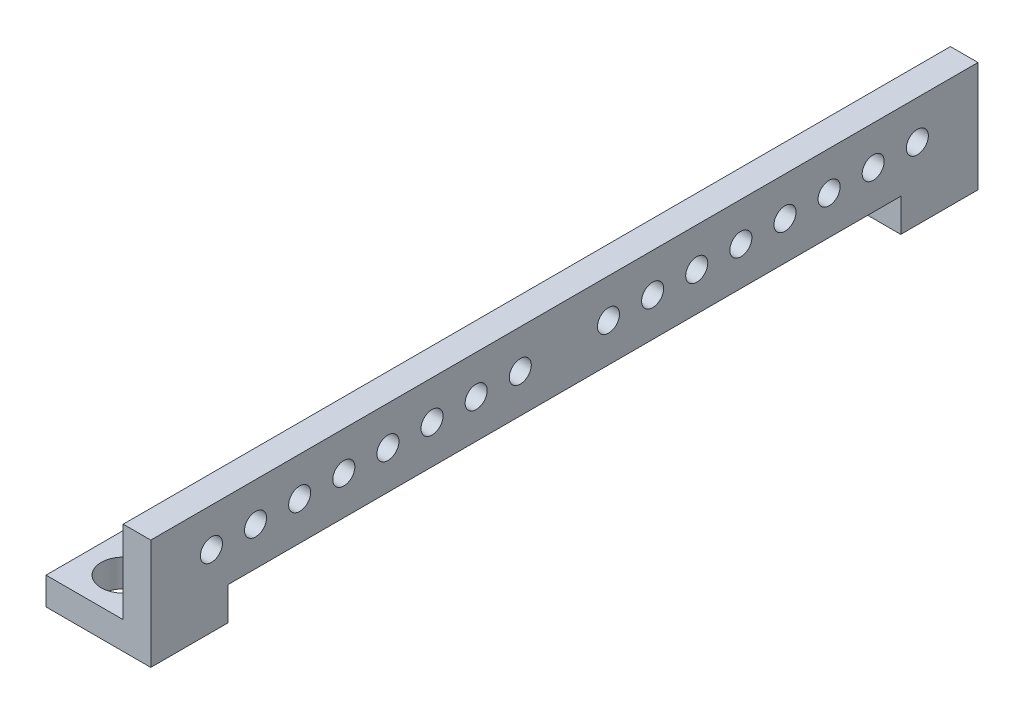
SolidWorks part; units mm, degrees
ref_plane "Front Plane" through (0, 0, 0) normal (0, 0, 1) x (1, 0, 0)
ref_plane "Top Plane" through (0, 0, 0) normal (0, 1, 0) x (1, 0, 0)
ref_plane "Right Plane" through (0, 0, 0) normal (1, 0, 0) x (0, 0, -1)
sketch "Sketch1" plane through (0, 0, 0) normal (1, 0, 0) x (0, 0, -1)
  line L0 (61, 0) -> (75, 0)
  line L1 (-75, 0) -> (-61, 0)
  line L2 (-75, 0) -> (-75, 20)
  line L3 (-75, 20) -> (75, 20)
  line L4 (75, 0) -> (75, 20)
  line L6 (-61, 0) -> (-61, 6)
  line L7 (-61, 6) -> (61, 6)
  line L8 (61, 0) -> (61, 6)
  line L12 (70, 13) -> (-70, 13) construction
  circle A2 centre (-16, 13) radius 2
  circle A3 centre (-24, 13) radius 2
  circle A4 centre (-32, 13) radius 2
  circle A5 centre (-40, 13) radius 2
  circle A6 centre (16, 13) radius 2
  circle A7 centre (24, 13) radius 2
  circle A8 centre (32, 13) radius 2
  circle A9 centre (40, 13) radius 2
  circle A10 centre (-48, 13) radius 2
  circle A11 centre (-56, 13) radius 2
  circle A12 centre (-64, 13) radius 2
  circle A13 centre (48, 13) radius 2
  circle A14 centre (56, 13) radius 2
  circle A15 centre (64, 13) radius 2
  circle A16 centre (-8, 13) radius 2
  circle A17 centre (8, 13) radius 2
  dimension "D11" = 4
  dimension "D12" = 4
  dimension "D13" = 4
  dimension "D14" = 4
  dimension "D15" = 4
  dimension "D16" = 4
  dimension "D17" = 4
  dimension "D18" = 4
  dimension "D23" = 8
  dimension "D24" = 8
  dimension "D25" = 16
  dimension "D27" = 4
  dimension "D28" = 4
  dimension "D29" = 4
  dimension "D30" = 4
  dimension "D31" = 4
  dimension "D32" = 4
  dimension "D33" = 8
  dimension "D34" = 8
  dimension "D35" = 8
  dimension "D36" = 8
  dimension "D37" = 8
  dimension "D38" = 8
  dimension "D39" = 4
  dimension "D40" = 8
  dimension "D41" = 8
  dimension "D42" = 4
  dimension "D1" = 150
  dimension "D2" = 20
  dimension "D3" = 0
  dimension "D4" = 6
  dimension "D5" = 14
  dimension "D6" = 14
  dimension "D7" = 61
  dimension "D8" = 5
  dimension "D9" = 5
  dimension "D10" = 7
  dimension "D19" = 8
  dimension "D20" = 8
  dimension "D21" = 8
  dimension "D22" = 8
  dimension "D26" = 16
extrude "Boss-Extrude1" add sketch "Sketch1" along normal blind 5
sketch "Sketch2" plane through (0, 0, 0) normal (-1, 0, 0) x (0, 0, 1)
  line L0 (-61, 6) -> (-61, 0) construction
  line L1 (-75, 0) -> (-61, 0)
  line L2 (-75, 0) -> (-75, 5)
  line L3 (-75, 5) -> (-61, 5)
  line L4 (-61, 0) -> (-61, 5)
  line L5 (75, 20) -> (75, 0) construction
  line L6 (61, 0) -> (75, 0)
  line L7 (61, 0) -> (61, 5)
  line L8 (61, 5) -> (75, 5)
  line L9 (75, 0) -> (75, 5)
  dimension "D1" = 5
  dimension "D2" = 5
extrude "Boss-Extrude2" add sketch "Sketch2" along normal blind 14
sketch "Sketch3" plane through (0, 0, 0) normal (0, -1, 0) x (-1, 0, 0)
  line L0 (-5, -75) -> (14, -75) construction
  line L1 (-5, 75) -> (14, 75) construction
  line L2 (14, 75) -> (14, 61) construction
  line L3 (14, -61) -> (14, -75) construction
  circle A0 centre (7, -68) radius 4
  circle A1 centre (7, 68) radius 4
  dimension "D2" = 8
  dimension "D3" = 7
  dimension "D4" = 8
  dimension "D5" = 7
  dimension "D6" = 7
  dimension "D1" = 7
extrude "Cut-Extrude1" cut sketch "Sketch3" against normal blind 25
